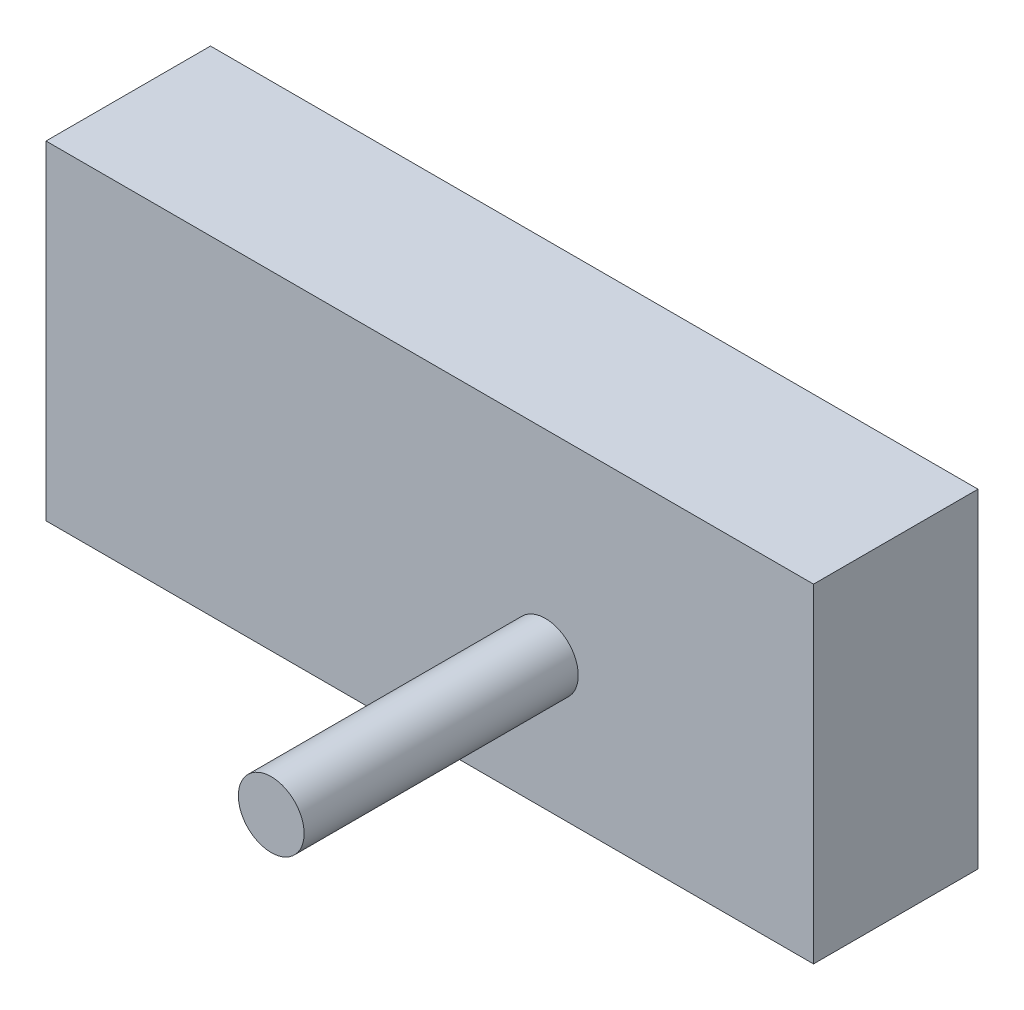
SolidWorks part; units mm, degrees
ref_plane "Ön Düzlem" through (0, 0, 0) normal (0, 0, 1) x (1, 0, 0)
ref_plane "Üst Düzlem" through (0, 0, 0) normal (0, 1, 0) x (1, 0, 0)
ref_plane "Sağ Düzlem" through (0, 0, 0) normal (1, 0, 0) x (0, 0, -1)
sketch "Çizim2" plane through (0, 0, 0) normal (0, 0, 1) x (1, 0, 0)
  line L1 (-47.7419, 29.8387) -> (92.2581, 29.8387)
  line L2 (-47.7419, 29.8387) -> (-47.7419, -30.1613)
  line L3 (-47.7419, -30.1613) -> (92.2581, -30.1613)
  line L4 (92.2581, 29.8387) -> (92.2581, -30.1613)
  dimension "D1" = 60
  dimension "D2" = 140
extrude "Yükseklik-Ekstrüzyon2" add sketch "Çizim2" along normal blind 30
sketch "Çizim3" plane through (0, 0, 30) normal (0, 0, 1) x (1, 0, 0)
  circle A0 centre (43.3422, -6.0313) radius 6
  dimension "D1" = 12
extrude "Yükseklik-Ekstrüzyon3" add sketch "Çizim3" along normal blind 50
